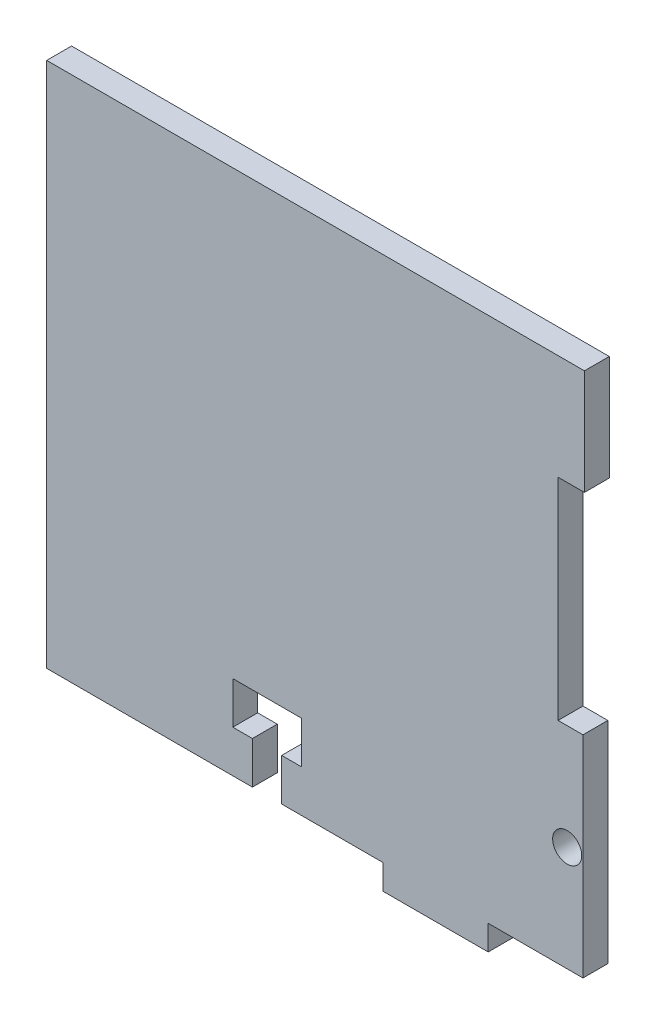
SolidWorks part; units mm, degrees
ref_plane "Front Plane" through (0, 0, 0) normal (0, 0, 1) x (1, 0, 0)
ref_plane "Top Plane" through (0, 0, 0) normal (0, 1, 0) x (1, 0, 0)
ref_plane "Right Plane" through (0, 0, 0) normal (1, 0, 0) x (0, 0, -1)
sketch "Sketch1" plane through (0, 0, 0) normal (0, 0, 1) x (1, 0, 0)
  line L1 (49.6283, 31.75) -> (111.125, 31.75)
  line L2 (111.125, 31.75) -> (114.475, 31.75)
  line L4 (114.3, -18.2294) -> (114.3, -6.35)
  line L27 (72.0725, -21.59) -> (80.3275, -21.59)
  line L28 (80.3275, -26.67) -> (80.3275, -21.59)
  line L29 (77.9653, -26.67) -> (80.3275, -26.67)
  line L30 (72.0725, -26.67) -> (74.4347, -26.67)
  line L31 (74.4347, -31.75) -> (74.4347, -26.67)
  line L32 (77.9653, -31.75) -> (77.9653, -26.67)
  line L33 (72.0725, -26.67) -> (72.0725, -21.59)
  line L35 (49.6283, -31.75) -> (74.4347, -31.75)
  line L36 (77.9653, -31.75) -> (88.1951, -31.75)
  line L37 (114.475, 31.75) -> (114.475, 19.05)
  line L38 (111.125, -31.75) -> (114.3, -31.75)
  line L39 (114.3, -31.75) -> (114.3, -19.8706)
  line L40 (102.87, -31.75) -> (111.125, -31.75)
  line L41 (114.475, 19.05) -> (111.3, 19.05)
  line L43 (114.3, -6.35) -> (111.3, -6.35)
  line L44 (111.3, 19.05) -> (111.3, -6.35)
  line L56 (88.1951, -31.75) -> (90.17, -31.75)
  line L57 (114.3, -18.2294) -> (114.3, -19.8706)
  line L58 (49.6283, 31.75) -> (49.6283, -31.75)
  line L59 (90.17, -31.75) -> (90.17, -34.75)
  line L60 (90.17, -34.75) -> (102.87, -34.75)
  line L61 (102.87, -31.75) -> (102.87, -34.75)
  circle A1 centre (112.395, -19.05) radius 1.7526
  dimension "D15" = 3
  dimension "D13" = 1.905
  dimension "D2" = 31.75
  dimension "D3" = 63.5
  dimension "D4" = 3
  dimension "D5" = 25.4
  dimension "D20" = 12.7
  dimension "D21" = 11.43
extrude "Boss-Extrude1" add sketch "Sketch1" along normal blind 3
